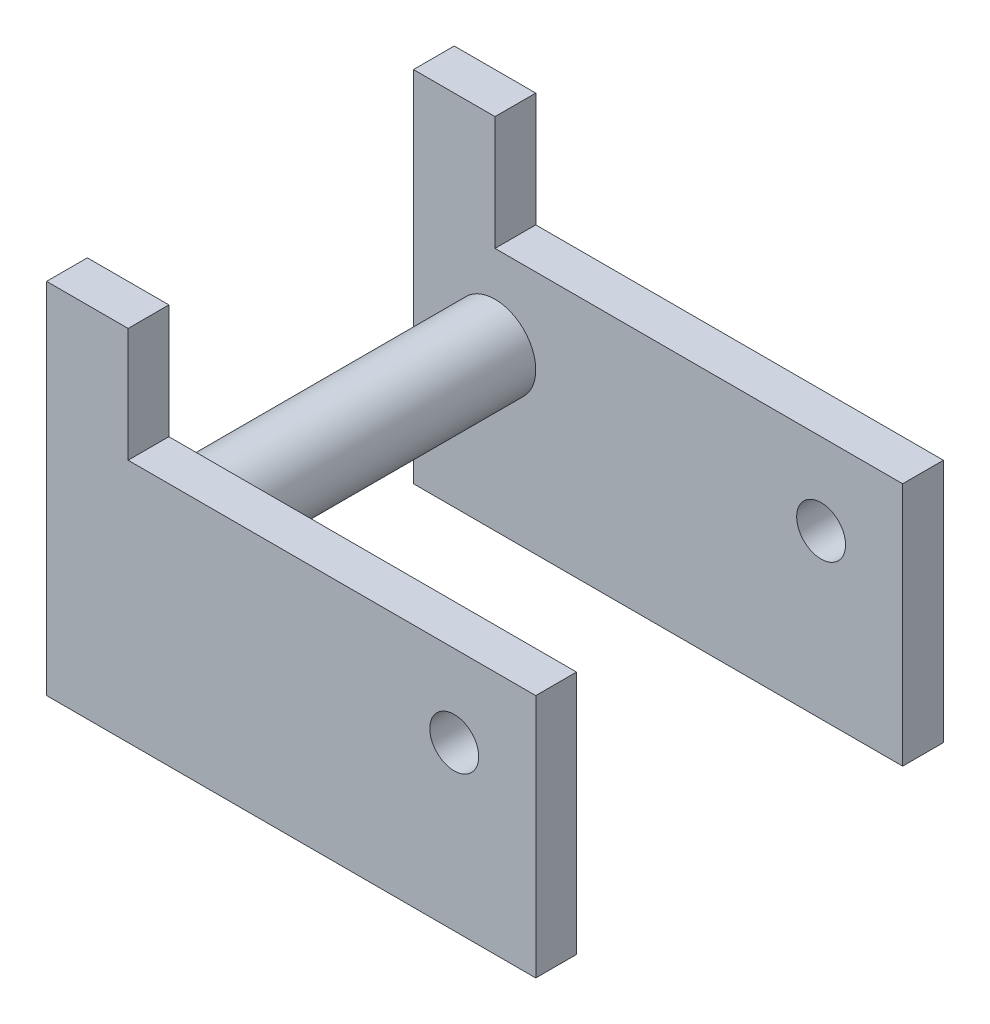
SolidWorks part; units mm, degrees
ref_plane "Front Plane" through (0, 0, 0) normal (0, 0, 1) x (1, 0, 0)
ref_plane "Top Plane" through (0, 0, 0) normal (0, 1, 0) x (1, 0, 0)
ref_plane "Right Plane" through (0, 0, 0) normal (1, 0, 0) x (0, 0, -1)
sketch "Sketch1" plane through (0, 0, 0) normal (0, 0, 1) x (1, 0, 0)
  line L1 (0, 0) -> (-38.1, 0)
  line L2 (0, 0) -> (0, 19.05)
  line L3 (0, 19.05) -> (-31.75, 19.05)
  line L4 (-38.1, 0) -> (-38.1, 6.35)
  line L6 (-38.1, 6.35) -> (-38.1, 27.94)
  line L7 (-38.1, 27.94) -> (-31.75, 27.94)
  line L8 (-31.75, 19.05) -> (-31.75, 27.94)
  dimension "D1" = 38.1
  dimension "D2" = 21.59
  dimension "D3" = 19.05
  dimension "D4" = 6.35
extrude "Boss-Extrude1" add sketch "Sketch1" along normal blind 31.75
sketch "Sketch2" plane through (0, 27.94, 0) normal (0, 1, 0) x (1, 0, 0)
  line L0 (-38.1, -31.75) -> (-38.1, 0) construction
  line L1 (-38.1, -3.175) -> (0, -3.175)
  line L2 (-38.1, -3.175) -> (-38.1, -28.575)
  line L3 (-38.1, -28.575) -> (0, -28.575)
  line L4 (0, -3.175) -> (0, -28.575)
  line L5 (0, -31.75) -> (0, 0) construction
  line L6 (-31.75, -31.75) -> (-38.1, -31.75) construction
  dimension "D1" = 25.4
  dimension "D2" = 3.175
extrude "Cut-Extrude1" cut sketch "Sketch2" against normal up to surface (27.94 mm away) up to face at (-19.05, 0, 15.875)
sketch "Sketch3" plane through (0, 0, 3.175) normal (0, 0, 1) x (1, 0, 0)
  line L0 (-38.1, 0) -> (-38.1, 27.94) construction
  line L2 (-38.1, 0) -> (0, 0) construction
  circle A1 centre (-31.75, 12.446) radius 3.175
  dimension "D4" = 6.35
  dimension "D5" = 12.446
  dimension "D6" = 6.35
extrude "Boss-Extrude2" add sketch "Sketch3" along normal up to surface (25.4 mm away) up to face at (-23.2833, 15.6633, 28.575)
sketch "Sketch5" plane through (0, 0, 31.75) normal (0, 0, 1) x (1, 0, 0)
  line L0 (0, 0) -> (0, 19.05) construction
  line L1 (-38.1, 0) -> (0, 0) construction
  circle A0 centre (-6.35, 12.7) radius 1.905
  dimension "D1" = 3.81
  dimension "D2" = 6.35
  dimension "D3" = 12.7
extrude "Cut-Extrude2" cut sketch "Sketch5" against normal through all
